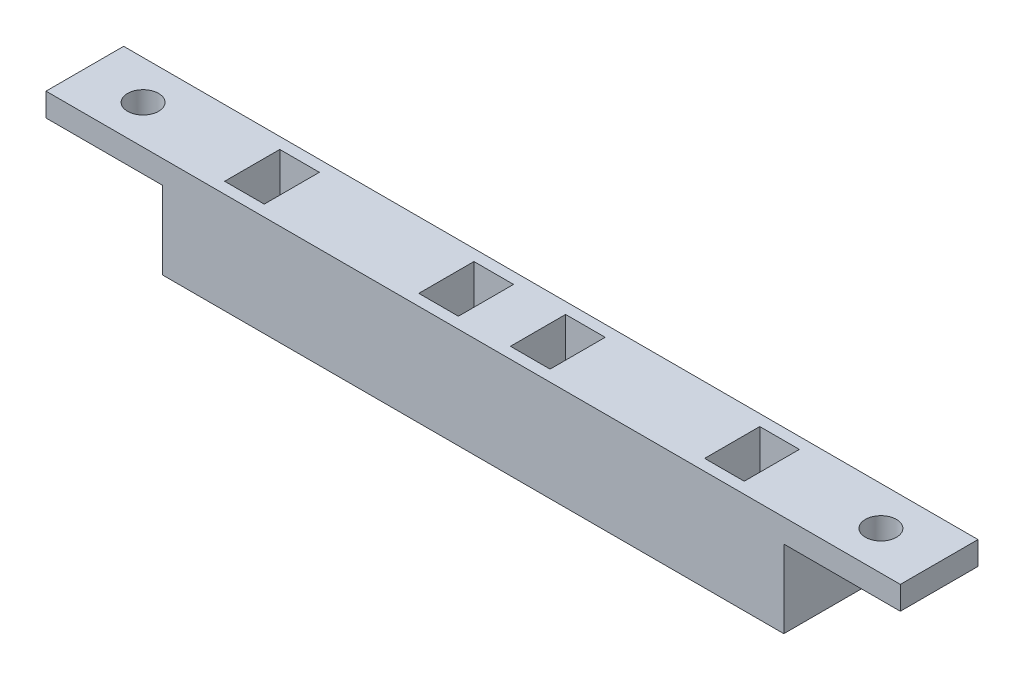
SolidWorks part; units mm, degrees
ref_plane "Front Plane" through (0, 0, 0) normal (0, 0, 1) x (1, 0, 0)
ref_plane "Top Plane" through (0, 0, 0) normal (0, 1, 0) x (1, 0, 0)
ref_plane "Right Plane" through (0, 0, 0) normal (1, 0, 0) x (0, 0, -1)
sketch "Sketch1" plane through (0, 0, 0) normal (0, 1, 0) x (1, 0, 0)
  line L1 (-72.863, 14.6132) -> (7.137, 14.6132)
  line L2 (-72.863, 14.6132) -> (-72.863, 4.6132)
  line L3 (-72.863, 4.6132) -> (7.137, 4.6132)
  line L4 (7.137, 14.6132) -> (7.137, 4.6132)
  dimension "D1" = 80
  dimension "D2" = 10
extrude "Boss-Extrude1" add sketch "Sketch1" along normal blind 10
sketch "Sketch2" plane through (0, 10, 0) normal (0, 1, 0) x (1, 0, 0)
  line L0 (-32.863, 14.6132) -> (-32.863, 4.6132) construction
  line L1 (-24.613, 20.3284) -> (-24.613, -1.807) construction
  line L2 (7.137, 14.6132) -> (-72.863, 14.6132) construction
  line L3 (-24.613, 12.9632) -> (-29.313, 12.9632)
  line L4 (-24.613, 12.9632) -> (-24.613, 6.2632)
  line L5 (-24.613, 6.2632) -> (-29.313, 6.2632)
  line L6 (-29.313, 12.9632) -> (-29.313, 6.2632)
  line L7 (-72.863, 4.6132) -> (7.137, 4.6132) construction
  line L8 (7.137, 9.6132) -> (-29.313, 9.6132) construction
  line L9 (7.137, 4.6132) -> (7.137, 14.6132) construction
  line L10 (-41.113, 12.9632) -> (-41.113, 6.2632)
  line L11 (-41.113, 6.2632) -> (-36.413, 6.2632)
  line L12 (-36.413, 12.9632) -> (-36.413, 6.2632)
  line L13 (-41.113, 12.9632) -> (-36.413, 12.9632)
  line L14 (0.387, 6.2632) -> (-4.313, 6.2632)
  line L15 (-4.313, 12.9632) -> (-4.313, 6.2632)
  line L16 (0.387, 12.9632) -> (0.387, 6.2632)
  line L17 (0.387, 12.9632) -> (-4.313, 12.9632)
  line L18 (-66.113, 12.9632) -> (-66.113, 6.2632)
  line L19 (-66.113, 12.9632) -> (-61.413, 12.9632)
  line L20 (-66.113, 6.2632) -> (-61.413, 6.2632)
  line L21 (-61.413, 12.9632) -> (-61.413, 6.2632)
  dimension "D1" = 8.25
  dimension "D2" = 4.7
  dimension "D3" = 6.7
  dimension "D4" = 2
  dimension "D5" = 2
extrude "Cut-Extrude1" cut sketch "Sketch2" against normal blind 7
sketch "Sketch3" plane through (0, 3, 0) normal (0, 1, 0) x (1, 0, 0)
  line L5 (-41.113, 12.9632) -> (-36.413, 12.9632)
  line L6 (-41.113, 12.9632) -> (-41.113, 6.2632)
  line L7 (-41.113, 6.2632) -> (-36.413, 6.2632)
  line L8 (-36.413, 12.9632) -> (-36.413, 6.2632)
sketch "Sketch4" plane through (0, 0, 0) normal (0, -1, 0) x (1, 0, 0)
  line L0 (-41.113, -12.9632) -> (-36.413, -12.9632) construction
  line L9 (-41.113, -6.2632) -> (-36.413, -6.2632) construction
  line L10 (-42.413, -5.9632) -> (-35.113, -5.9632)
  line L11 (-42.413, -5.9632) -> (-42.413, -13.2632)
  line L12 (-42.413, -13.2632) -> (-35.113, -13.2632)
  line L13 (-35.113, -5.9632) -> (-35.113, -13.2632)
  line L15 (-36.413, -12.9632) -> (-36.413, -6.2632) construction
  line L16 (-41.113, -12.9632) -> (-41.113, -6.2632) construction
  dimension "D1" = 0.3
  dimension "D5" = 0.3
  dimension "D7" = 1.3
  dimension "D8" = 1.3
loft "Cut-Loft1" cut profiles "Sketch3", "Sketch4"
sketch "Sketch5" plane through (0, 3, 0) normal (0, 1, 0) x (1, 0, 0)
  line L1 (-66.113, 12.9632) -> (-61.413, 12.9632)
  line L2 (-66.113, 12.9632) -> (-66.113, 6.2632)
  line L3 (-66.113, 6.2632) -> (-61.413, 6.2632)
  line L4 (-61.413, 12.9632) -> (-61.413, 6.2632)
sketch "Sketch6" plane through (0, 0, 0) normal (0, -1, 0) x (1, 0, 0)
  line L0 (-66.113, -6.2632) -> (-61.413, -6.2632) construction
  line L1 (-67.413, -5.9632) -> (-60.113, -5.9632)
  line L2 (-67.413, -5.9632) -> (-67.413, -13.2632)
  line L3 (-67.413, -13.2632) -> (-60.113, -13.2632)
  line L4 (-60.113, -5.9632) -> (-60.113, -13.2632)
  line L5 (-66.113, -12.9632) -> (-61.413, -12.9632) construction
  line L6 (-61.413, -12.9632) -> (-61.413, -6.2632) construction
  line L7 (-66.113, -12.9632) -> (-66.113, -6.2632) construction
  dimension "D1" = 0.3
  dimension "D2" = 0.3
  dimension "D3" = 1.3
  dimension "D4" = 1.3
loft "Cut-Loft2" cut profiles "Sketch5", "Sketch6"
sketch "Sketch8" plane through (0, 3, 0) normal (0, 1, 0) x (1, 0, 0)
  line L1 (-29.313, 12.9632) -> (-24.613, 12.9632)
  line L2 (-29.313, 12.9632) -> (-29.313, 6.2632)
  line L3 (-29.313, 6.2632) -> (-24.613, 6.2632)
  line L4 (-24.613, 12.9632) -> (-24.613, 6.2632)
sketch "Sketch9" plane through (0, 0, 0) normal (0, -1, 0) x (1, 0, 0)
  line L0 (-29.313, -6.2632) -> (-24.613, -6.2632) construction
  line L1 (-30.613, -5.9632) -> (-23.313, -5.9632)
  line L2 (-30.613, -5.9632) -> (-30.613, -13.2632)
  line L3 (-30.613, -13.2632) -> (-23.313, -13.2632)
  line L4 (-23.313, -5.9632) -> (-23.313, -13.2632)
  line L5 (-29.313, -12.9632) -> (-24.613, -12.9632) construction
  line L6 (-24.613, -12.9632) -> (-24.613, -6.2632) construction
  line L7 (-29.313, -12.9632) -> (-29.313, -6.2632) construction
  dimension "D1" = 0.3
  dimension "D2" = 0.3
  dimension "D3" = 1.3
  dimension "D4" = 1.3
loft "Cut-Loft3" cut profiles "Sketch8", "Sketch9"
sketch "Sketch10" plane through (0, 3, 0) normal (0, 1, 0) x (1, 0, 0)
  line L1 (-4.313, 12.9632) -> (0.387, 12.9632)
  line L2 (-4.313, 12.9632) -> (-4.313, 6.2632)
  line L3 (-4.313, 6.2632) -> (0.387, 6.2632)
  line L4 (0.387, 12.9632) -> (0.387, 6.2632)
sketch "Sketch11" plane through (0, 0, 0) normal (0, -1, 0) x (1, 0, 0)
  line L0 (-4.313, -6.2632) -> (0.387, -6.2632) construction
  line L1 (-5.613, -5.9632) -> (1.687, -5.9632)
  line L2 (-5.613, -5.9632) -> (-5.613, -13.2632)
  line L3 (-5.613, -13.2632) -> (1.687, -13.2632)
  line L4 (1.687, -5.9632) -> (1.687, -13.2632)
  line L5 (-4.313, -12.9632) -> (0.387, -12.9632) construction
  line L6 (0.387, -12.9632) -> (0.387, -6.2632) construction
  line L7 (-4.313, -12.9632) -> (-4.313, -6.2632) construction
  dimension "D1" = 0.3
  dimension "D2" = 0.3
  dimension "D3" = 1.3
  dimension "D4" = 1.3
loft "Cut-Loft4" cut profiles "Sketch10", "Sketch11"
sketch "Sketch12" plane through (0, 10, 0) normal (0, 1, 0) x (1, 0, 0)
  line L0 (-72.863, 14.6132) -> (-72.863, 4.6132) construction
  line L1 (-87.863, 14.6132) -> (22.137, 14.6132)
  line L2 (-87.863, 14.6132) -> (-87.863, 4.6132)
  line L3 (-87.863, 4.6132) -> (22.137, 4.6132)
  line L4 (22.137, 14.6132) -> (22.137, 4.6132)
  line L5 (7.137, 4.6132) -> (7.137, 14.6132) construction
  line L7 (-66.113, 12.9632) -> (-61.413, 12.9632)
  line L8 (-66.113, 12.9632) -> (-66.113, 6.2632)
  line L9 (-66.113, 6.2632) -> (-61.413, 6.2632)
  line L10 (-61.413, 12.9632) -> (-61.413, 6.2632)
  line L11 (-41.113, 12.9632) -> (-36.413, 12.9632)
  line L12 (-41.113, 12.9632) -> (-41.113, 6.2632)
  line L13 (-41.113, 6.2632) -> (-36.413, 6.2632)
  line L14 (-36.413, 12.9632) -> (-36.413, 6.2632)
  line L15 (-29.313, 12.9632) -> (-24.613, 12.9632)
  line L16 (-29.313, 12.9632) -> (-29.313, 6.2632)
  line L17 (-29.313, 6.2632) -> (-24.613, 6.2632)
  line L18 (-24.613, 12.9632) -> (-24.613, 6.2632)
  line L19 (-4.313, 12.9632) -> (0.387, 12.9632)
  line L20 (-4.313, 12.9632) -> (-4.313, 6.2632)
  line L21 (-4.313, 6.2632) -> (0.387, 6.2632)
  line L22 (0.387, 12.9632) -> (0.387, 6.2632)
  dimension "D1" = 15
  dimension "D2" = 15
extrude "Boss-Extrude2" add sketch "Sketch12" along normal blind 3
sketch "Sketch13" plane through (0, 13, 0) normal (0, 1, 0) x (1, 0, 0)
  line L0 (-61.413, 12.9632) -> (-66.113, 12.9632) construction
  line L1 (-66.313, 13.1632) -> (-61.213, 13.1632)
  line L2 (-66.313, 13.1632) -> (-66.313, 6.0632)
  line L3 (-66.313, 6.0632) -> (-61.213, 6.0632)
  line L4 (-61.213, 13.1632) -> (-61.213, 6.0632)
  line L5 (-66.113, 6.2632) -> (-61.413, 6.2632) construction
  line L6 (-61.413, 6.2632) -> (-61.413, 12.9632) construction
  line L7 (-66.113, 12.9632) -> (-66.113, 6.2632) construction
  line L8 (-36.413, 12.9632) -> (-41.113, 12.9632) construction
  line L9 (-41.313, 13.1632) -> (-36.213, 13.1632)
  line L10 (-41.313, 13.1632) -> (-41.313, 6.0632)
  line L11 (-41.313, 6.0632) -> (-36.213, 6.0632)
  line L12 (-36.213, 13.1632) -> (-36.213, 6.0632)
  line L13 (-41.113, 6.2632) -> (-36.413, 6.2632) construction
  line L14 (-36.413, 6.2632) -> (-36.413, 12.9632) construction
  line L15 (-41.113, 12.9632) -> (-41.113, 6.2632) construction
  line L16 (-29.313, 12.9632) -> (-29.313, 6.2632) construction
  line L17 (-29.513, 13.1632) -> (-24.413, 13.1632)
  line L18 (-29.513, 13.1632) -> (-29.513, 6.0632)
  line L19 (-29.513, 6.0632) -> (-24.413, 6.0632)
  line L20 (-24.413, 13.1632) -> (-24.413, 6.0632)
  line L21 (-24.613, 6.2632) -> (-24.613, 12.9632) construction
  line L22 (-24.613, 12.9632) -> (-29.313, 12.9632) construction
  line L23 (-29.313, 6.2632) -> (-24.613, 6.2632) construction
  line L24 (0.387, 12.9632) -> (-4.313, 12.9632) construction
  line L25 (-4.513, 13.1632) -> (0.587, 13.1632)
  line L26 (-4.513, 13.1632) -> (-4.513, 6.0632)
  line L27 (-4.513, 6.0632) -> (0.587, 6.0632)
  line L28 (0.587, 13.1632) -> (0.587, 6.0632)
  line L29 (-4.313, 6.2632) -> (0.387, 6.2632) construction
  line L30 (0.387, 6.2632) -> (0.387, 12.9632) construction
  line L31 (-4.313, 12.9632) -> (-4.313, 6.2632) construction
  dimension "D1" = 0.2
  dimension "D2" = 0.2
  dimension "D3" = 0.2
  dimension "D4" = 0.2
  dimension "D5" = 0.2
  dimension "D6" = 0.2
  dimension "D7" = 0.2
  dimension "D8" = 0.2
  dimension "D9" = 0.2
  dimension "D10" = 0.2
  dimension "D11" = 0.2
  dimension "D12" = 0.2
  dimension "D13" = 0.2
  dimension "D14" = 0.2
  dimension "D15" = 0.2
  dimension "D16" = 0.2
extrude "Cut-Extrude2" cut sketch "Sketch13" against normal blind 5.5
sketch "Sketch14" plane through (0, 13, 0) normal (0, 1, 0) x (1, 0, 0)
  line L0 (22.137, 4.6132) -> (22.137, 14.6132) construction
  line L1 (-32.863, 23.8411) -> (-32.863, -5.985) construction
  circle A0 centre (14.637, 9.6132) radius 2
  circle A1 centre (-80.363, 9.6132) radius 2
  point P2 (22.137, 9.6132)
  dimension "D1" = 7.5
  dimension "D2" = 4
extrude "Cut-Extrude3" cut sketch "Sketch14" against normal blind 10
